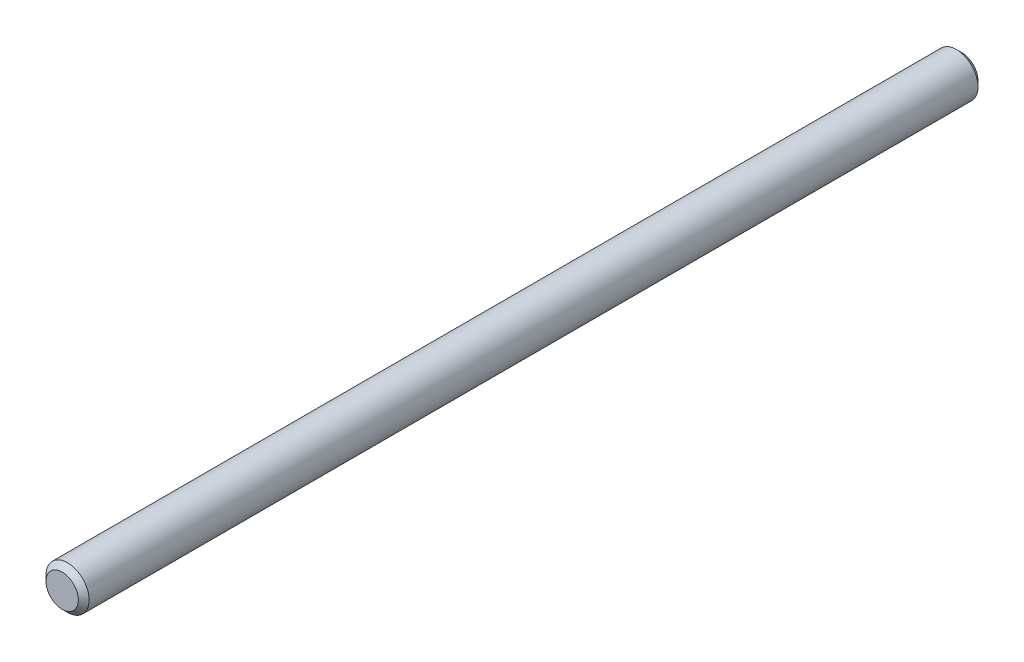
SolidWorks part; units mm, degrees
ref_plane "Piano frontale" through (0, 0, 0) normal (0, 0, 1) x (1, 0, 0)
ref_plane "Piano superiore" through (0, 0, 0) normal (0, 1, 0) x (1, 0, 0)
ref_plane "Piano destro" through (0, 0, 0) normal (1, 0, 0) x (0, 0, -1)
ref_plane "Plane1" through (0, 0, 99) normal (0, 0, -1) x (-1, 0, 0)
sketch "Schizzo1" plane through (0, 0, 99) normal (0, 0, 1) x (1, 0, 0)
  circle A0 centre (0, 0) radius 4
  dimension "D1" = 8
extrude "Estrusione-Estrusione1" add sketch "Schizzo1" along normal up to surface (167 mm away)
chamfer "Smusso1" distance 1 angle 45
